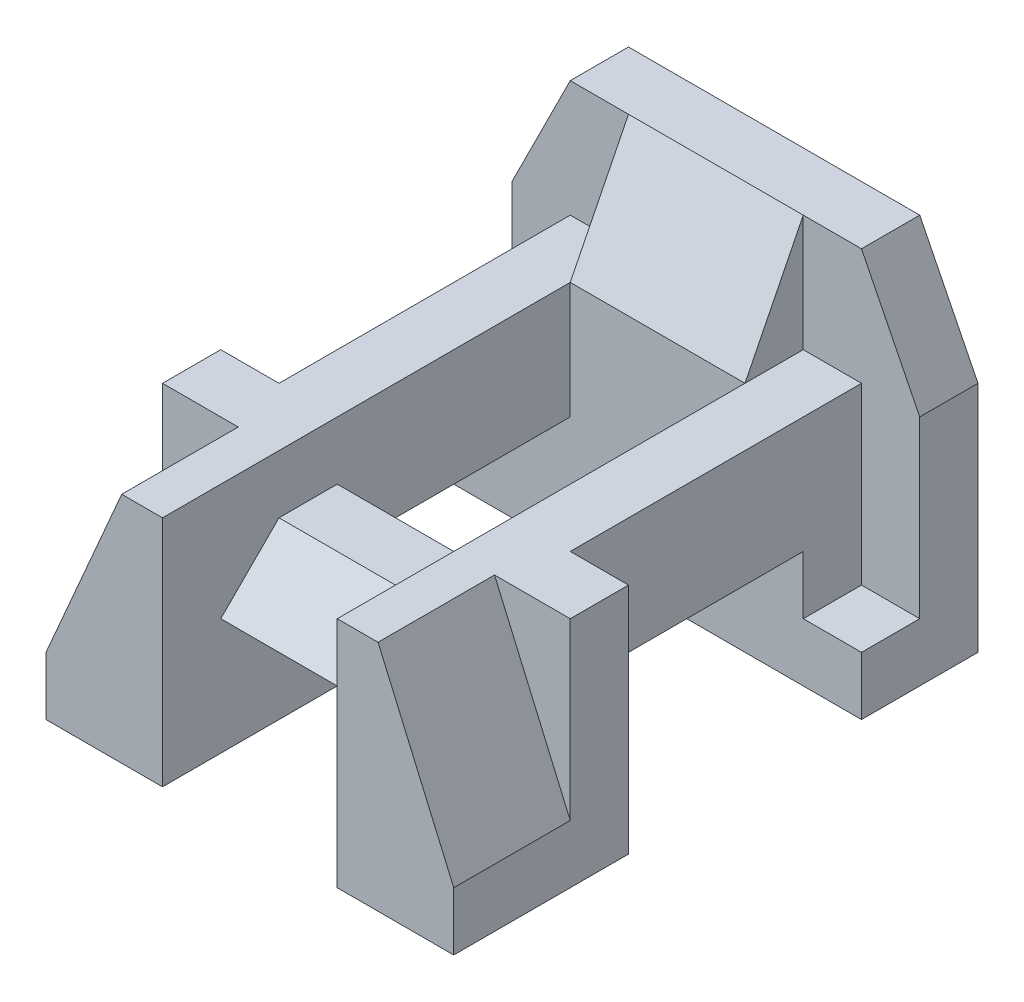
SolidWorks part; units mm, degrees
ref_plane "Front Plane" through (0, 0, 0) normal (0, 0, 1) x (1, 0, 0)
ref_plane "Top Plane" through (0, 0, 0) normal (0, 1, 0) x (1, 0, 0)
ref_plane "Right Plane" through (0, 0, 0) normal (1, 0, 0) x (0, 0, -1)
sketch "Sketch1" plane through (0, 0, 0) normal (0, 0, 1) x (1, 0, 0)
  line L1 (3.5, -3) -> (-3.5, -3)
  line L2 (3.5, -3) -> (3.5, 3)
  line L3 (3.5, 3) -> (-3.5, 3)
  line L4 (-3.5, -3) -> (-3.5, 3)
  line L5 (3.5, -3) -> (-3.5, 3) construction
  line L6 (3.5, 3) -> (-3.5, -3) construction
  point P0 (0, 0)
  dimension "D1" = 7
  dimension "D2" = 6
extrude "Boss-Extrude1" add sketch "Sketch1" along normal blind 9
sketch "Sketch2" plane through (0, 3, 0) normal (0, 1, 0) x (1, 0, 0)
  line L11 (3.5, -9) -> (-3.5, -9) construction
  line L16 (1.5, -9) -> (-1.5, -9)
  line L17 (1.5, -9) -> (1.5, -8)
  line L18 (1.5, -8) -> (-1.5, -8)
  line L19 (-1.5, -9) -> (-1.5, -8)
  dimension "D10" = 2
  dimension "D11" = 2
  dimension "D12" = 1
extrude "Cut-Extrude10" cut sketch "Sketch2" against normal through all
sketch "Sketch11" plane through (0, 0, 0) normal (0, 0, -1) x (-1, 0, 0)
  line L0 (-2.5, 3) -> (-3.5, 1)
  line L1 (-3.5, 3) -> (3.5, 3) construction
  line L2 (-3.5, -3) -> (-3.5, 3) construction
  line L3 (-3.5, 1) -> (-3.5, 3)
  line L4 (-3.5, 3) -> (-2.5, 3)
  line L5 (3.5, 3) -> (2.5, 3)
  line L6 (2.5, 3) -> (3.5, 1)
  line L7 (3.5, 3) -> (3.5, -3) construction
  line L8 (3.5, 1) -> (3.5, 3)
  dimension "D1" = 1
  dimension "D2" = 1
  dimension "D3" = 2
  dimension "D4" = 2
extrude "Cut-Extrude11" cut sketch "Sketch11" against normal blind 1
sketch "Sketch12" plane through (0, 3, 0) normal (0, 1, 0) x (1, 0, 0)
  line L0 (3.5, -1) -> (2.5, -1)
  line L1 (2.5, -1) -> (2.5, -2)
  line L2 (2.5, -2) -> (3.5, -2)
  line L3 (3.5, -9) -> (3.5, -1) construction
  line L4 (3.5, -2) -> (3.5, -1)
  line L5 (-3.5, -1) -> (-2.5, -1)
  line L6 (-2.5, -1) -> (-2.5, -2)
  line L7 (-2.5, -2) -> (-3.5, -2)
  line L8 (-3.5, -9) -> (-3.5, -1) construction
  line L9 (-3.5, -2) -> (-3.5, -1)
  dimension "D1" = 1
  dimension "D2" = 1
extrude "Cut-Extrude12" cut sketch "Sketch12" against normal blind 5
sketch "Sketch13" plane through (0, 3, 0) normal (0, 1, 0) x (1, 0, 0)
  line L0 (3.5, -2) -> (2.5, -2)
  line L1 (2.5, -2) -> (2.5, -6)
  line L2 (2.5, -6) -> (3.5, -6)
  line L3 (3.5, -9) -> (3.5, -2) construction
  line L4 (3.5, -6) -> (3.5, -2)
  line L5 (-3.5, -2) -> (-2.5, -2)
  line L6 (-2.5, -2) -> (-2.5, -6)
  line L7 (-2.5, -6) -> (-3.5, -6)
  line L8 (-3.5, -9) -> (-3.5, -2) construction
  line L9 (-3.5, -6) -> (-3.5, -2)
  dimension "D1" = 4
  dimension "D2" = 4
extrude "Cut-Extrude13" cut sketch "Sketch13" against normal through all
sketch "Sketch14" plane through (0, 0, 9) normal (0, 0, 1) x (1, 0, 0)
  line L0 (3.5, 3) -> (2.5, 3)
  line L1 (3.5, 3) -> (1.5, 3) construction
  line L2 (2.5, 3) -> (3.5, -2)
  line L3 (3.5, -3) -> (3.5, 3) construction
  line L4 (3.5, -2) -> (3.5, 3)
  line L5 (-3.5, 3) -> (-2.5, 3)
  line L6 (-1.5, 3) -> (-3.5, 3) construction
  line L7 (-2.5, 3) -> (-3.5, -2)
  line L8 (-3.5, 3) -> (-3.5, -3) construction
  line L9 (-3.5, -2) -> (-3.5, 3)
  dimension "D1" = 1
  dimension "D2" = 1
extrude "Cut-Extrude14" cut sketch "Sketch14" against normal blind 2
sketch "Sketch15" plane through (0, 0, 8) normal (0, 0, 1) x (1, 0, 0)
  line L0 (-1.5, -3) -> (-1.5, -1)
  line L1 (-1.5, -3) -> (-1.5, 3) construction
  line L2 (-1.5, -1) -> (1.5, -1)
  line L3 (1.5, -3) -> (1.5, 3) construction
  line L4 (1.5, -1) -> (1.5, -3)
  line L5 (1.5, -3) -> (-1.5, -3)
  dimension "D1" = 2
extrude "Cut-Extrude17" cut sketch "Sketch15" against normal blind 6
sketch "Sketch18" plane through (0, 0, 8) normal (0, 0, 1) x (1, 0, 0)
  line L0 (1.5, 3) -> (1.5, 2)
  line L1 (1.5, -1) -> (1.5, 3) construction
  line L2 (1.5, 2) -> (-1.5, 2)
  line L3 (-1.5, -3) -> (-1.5, 3) construction
  line L4 (-1.5, 2) -> (-1.5, 3)
  line L5 (-1.5, 3) -> (1.5, 3)
  dimension "D1" = 1
extrude "Cut-Extrude18" cut sketch "Sketch18" against normal blind 6
sketch "Sketch19" plane through (0, 2, 0) normal (0, 1, 0) x (1, 0, 0)
  line L0 (-1.5, -7) -> (1.5, -7)
  line L1 (-1.5, -2) -> (-1.5, -9) construction
  line L2 (1.5, -2) -> (1.5, -8) construction
  line L3 (-1.5, -8) -> (1.5, -8) construction
  dimension "D1" = 1
ref_plane "Plane4" through (0, 2.3, 6.9) normal (0, -0.3162, -0.9487) x (-1, 0, 0)
sketch "Sketch20" plane through (0, 2.3, 6.9) normal (0, -0.3162, -0.9487) x (-1, 0, 0)
  line L0 (1.5, -0.3162) -> (1.5, -3.4785)
  line L1 (1.5, -3.4785) -> (-1.5, -3.4785)
  line L2 (-1.5, -3.4785) -> (-1.5, -0.3162)
  line L3 (-1.5, -0.3162) -> (1.5, -0.3162)
extrude "Cut-Extrude19" cut sketch "Sketch20" against normal blind 6
sketch "Sketch21" plane through (0, 2, 0) normal (0, 1, 0) x (1, 0, 0)
  line L0 (1.5, -2) -> (-1.5, -2)
  line L1 (-1.5, -2) -> (-1.5, -6)
  line L2 (-1.5, -2) -> (-1.5, -9) construction
  line L3 (-1.5, -6) -> (1.5, -6)
  line L4 (1.5, -2) -> (1.5, -7) construction
  line L5 (1.5, -6) -> (1.5, -2)
  dimension "D1" = 1
extrude "Cut-Extrude20" cut sketch "Sketch21" against normal through all
sketch "Sketch22" plane through (0, 0, 9) normal (0, 0, 1) x (1, 0, 0)
  line L0 (1.5, 2) -> (1.5, 1)
  line L1 (1.5, 2) -> (1.5, -1) construction
  line L2 (1.5, 1) -> (-1.5, 1)
  line L3 (-1.5, -1) -> (-1.5, 2) construction
  line L4 (-1.5, 1) -> (-1.5, 2)
  line L5 (-1.5, 2) -> (1.5, 2)
  line L6 (1.5, -1) -> (-1.5, -1) construction
  dimension "D1" = 2
extrude "Cut-Extrude22" cut sketch "Sketch22" against normal blind 6
sketch "Sketch23" plane through (0, 0, 9) normal (0, 0, 1) x (1, 0, 0)
  line L0 (3.5, 1) -> (-3.5, 1)
  line L1 (3.5, -2) -> (3.5, 3) construction
  line L2 (-3.5, 3) -> (-3.5, -2) construction
  line L3 (-3.5, 1) -> (-3.5, 3)
  line L4 (-3.5, 3) -> (3.5, 3)
  line L5 (3.5, 3) -> (3.5, 1)
  dimension "D1" = 2
extrude "Cut-Extrude24" cut sketch "Sketch23" against normal blind 7
sketch "Sketch24" plane through (0, 0, 9) normal (0, 0, 1) x (1, 0, 0)
  line L0 (2.2, 1) -> (3.5, -2)
  line L1 (1.5, 1) -> (2.9, 1) construction
  line L2 (3.5, -2) -> (2.9, 1)
  line L3 (2.9, 1) -> (2.2, 1)
  line L4 (-2.2, 1) -> (-2.9, 1)
  line L5 (-2.9, 1) -> (-1.5, 1) construction
  line L6 (-2.9, 1) -> (-3.5, -2)
  line L7 (-3.5, -2) -> (-2.2, 1)
  line L8 (1.5, 0) -> (-1.5, 0)
  line L9 (1.5, 1) -> (1.5, -1) construction
  line L10 (-1.5, -1) -> (-1.5, 1) construction
  line L11 (-1.5, 0) -> (-1.5, 1)
  line L12 (-1.5, 1) -> (1.5, 1)
  line L13 (1.5, 1) -> (1.5, 0)
extrude "Cut-Extrude25" cut sketch "Sketch24" against normal blind 2
sketch "Sketch25" plane through (0, 0, 7) normal (0, 0, 1) x (1, 0, 0)
  line L0 (1.5, 1) -> (1.5, 0)
  line L1 (1.5, 0) -> (-1.5, 0)
  line L2 (-1.5, 0) -> (-1.5, 1)
  line L3 (-1.5, 1) -> (1.5, 1)
extrude "Cut-Extrude26" cut sketch "Sketch25" against normal blind 2
sketch "Sketch26" plane through (0, 3, 0) normal (0, 1, 0) x (1, 0, 0)
  line L0 (1.5, -1) -> (-1.5, -1)
  line L1 (2.5, 0) -> (-2.5, 0) construction
  dimension "D1" = 1
  dimension "D2" = 1
  dimension "D3" = 1
sketch "Sketch27" plane through (0, 0, 2) normal (0, 0, 1) x (1, 0, 0)
  line L0 (1.5, 1) -> (-1.5, 1)
ref_plane "Plane8" through (0, 1, 2) normal (0, 0.4472, 0.8944) x (1, 0, 0)
sketch "Sketch28" plane through (0, 1, 2) normal (0, 0.4472, 0.8944) x (1, 0, 0)
  line L0 (1.5, 2.2361) -> (1.5, 0)
  line L1 (1.5, 0) -> (-1.5, 0)
  line L2 (-1.5, 0) -> (-1.5, 2.2361)
  line L3 (-1.5, 2.2361) -> (1.5, 2.2361)
extrude "Cut-Extrude27" cut sketch "Sketch28" along normal blind 2
sketch "Sketch29" plane through (2.5, 0, 0) normal (1, 0, 0) x (0, 0, -1)
  line L0 (-1, 3) -> (-1, 1)
  line L1 (-1, 1) -> (-2, 1)
  line L2 (-2, 1) -> (-2, 3)
  line L3 (-2, 3) -> (-1, 3)
extrude "Cut-Extrude28" cut sketch "Sketch29" against normal blind 1
sketch "Sketch30" plane through (-2.5, 0, 0) normal (-1, 0, 0) x (0, 0, 1)
  line L0 (1, 3) -> (2, 3)
  line L1 (2, 3) -> (2, 1)
  line L2 (2, 1) -> (1, 1)
  line L3 (1, 1) -> (1, 3)
extrude "Cut-Extrude29" cut sketch "Sketch30" against normal blind 1
sketch "Sketch31" plane through (2.5, 0, 0) normal (1, 0, 0) x (0, 0, -1)
  line L1 (-2, -3) -> (-5, -3)
  line L2 (-2, -3) -> (-2, -1)
  line L3 (-2, -1) -> (-5, -1)
  line L4 (-5, -3) -> (-5, -1)
  dimension "D1" = 2
  dimension "D2" = 3
extrude "Cut-Extrude30" cut sketch "Sketch31" against normal blind 40
sketch "Sketch32" plane through (0, 0, 0) normal (0, 1, 0) x (1, 0, 0)
  line L0 (-1.5, -6) -> (-1.5, -7.6667) construction
  line L5 (1.5, -6) -> (1.5, -7.6667) construction
  point P0 (-1.5, -7)
  point P1 (1.5, -7)
  dimension "D1" = 1
sketch "Sketch33" plane through (-1.5, 0, 0) normal (1, 0, 0) x (0, 0, -1)
  line L0 (-7, 0) -> (-8, -1)
  line L1 (-8, -1) -> (-8.4357, 0.3621)
  line L2 (-8.4357, 0.3621) -> (-7, 0)
extrude "Cut-Extrude31" cut sketch "Sketch33" along normal blind 3
